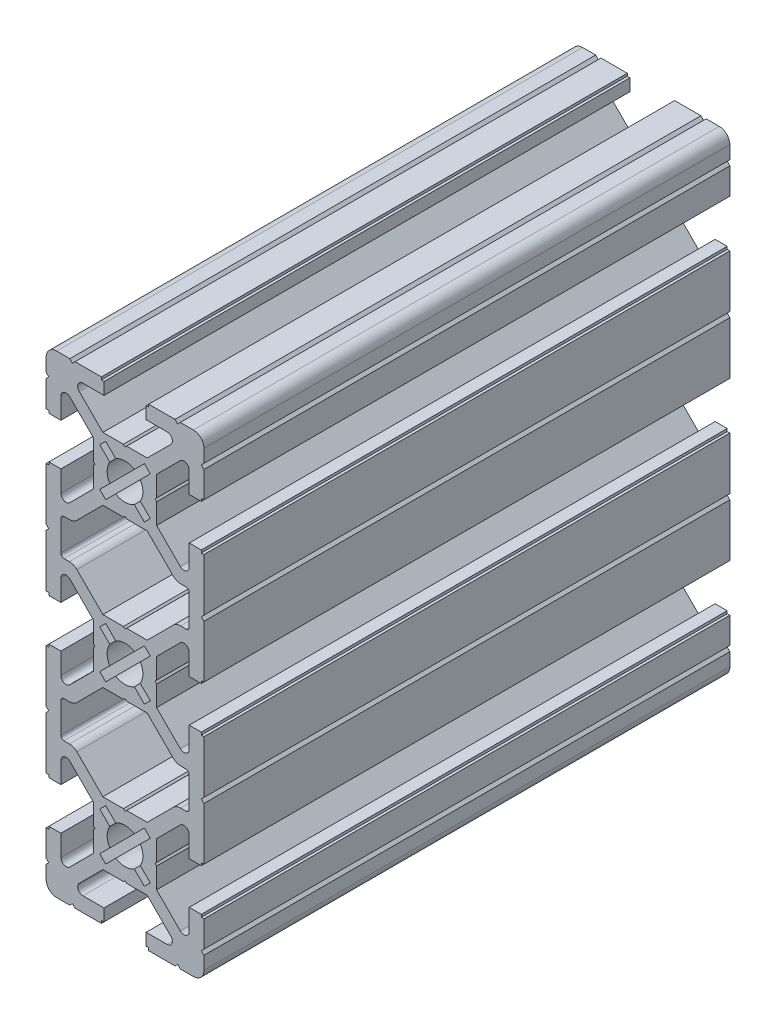
SolidWorks part; units mm, degrees
ref_plane "Ön Düzlem" through (0, 0, 0) normal (0, 0, 1) x (1, 0, 0)
ref_plane "Üst Düzlem" through (0, 0, 0) normal (0, 1, 0) x (1, 0, 0)
ref_plane "Sağ Düzlem" through (0, 0, 0) normal (1, 0, 0) x (0, 0, -1)
ref_plane "Düzlem1" through (0, 0, 100) normal (0, 0, 1) x (1, 0, 0)
sketch "Çizim1" plane through (0, 0, 100) normal (0, 0, 1) x (1, 0, 0)
  line L0 (-2.9023, 31.771) -> (-4.8083, 33.677)
  line L1 (-4.8083, 33.677) -> (-3.677, 34.8083)
  line L2 (-3.677, 34.8083) -> (-1.771, 32.9023)
  line L3 (1.771, 32.9023) -> (3.677, 34.8083)
  line L4 (3.677, 34.8083) -> (4.8083, 33.677)
  line L5 (4.8083, 33.677) -> (2.9023, 31.771)
  line L6 (2.9023, 28.229) -> (4.8083, 26.323)
  line L7 (4.8083, 26.323) -> (3.677, 25.1917)
  line L8 (3.677, 25.1917) -> (1.771, 27.0977)
  line L9 (-1.771, 27.0977) -> (-3.677, 25.1917)
  line L10 (-3.677, 25.1917) -> (-4.8083, 26.323)
  line L11 (-4.8083, 26.323) -> (-2.9023, 28.229)
  line L12 (-2.9023, 1.771) -> (-4.8083, 3.677)
  line L13 (-4.8083, 3.677) -> (-3.677, 4.8083)
  line L14 (-3.677, 4.8083) -> (-1.771, 2.9023)
  line L15 (1.771, 2.9023) -> (3.677, 4.8083)
  line L16 (3.677, 4.8083) -> (4.8083, 3.677)
  line L17 (4.8083, 3.677) -> (2.9023, 1.771)
  line L18 (2.9023, -1.771) -> (4.8083, -3.677)
  line L19 (4.8083, -3.677) -> (3.677, -4.8083)
  line L20 (3.677, -4.8083) -> (1.771, -2.9023)
  line L21 (-1.771, -2.9023) -> (-3.677, -4.8083)
  line L22 (-3.677, -4.8083) -> (-4.8083, -3.677)
  line L23 (-4.8083, -3.677) -> (-2.9023, -1.771)
  line L24 (-2.9023, -28.229) -> (-4.8083, -26.323)
  line L25 (-4.8083, -26.323) -> (-3.677, -25.1917)
  line L26 (-3.677, -25.1917) -> (-1.771, -27.0977)
  line L27 (1.771, -27.0977) -> (3.677, -25.1917)
  line L28 (3.677, -25.1917) -> (4.8083, -26.323)
  line L29 (4.8083, -26.323) -> (2.9023, -28.229)
  line L30 (2.9023, -31.771) -> (4.8083, -33.677)
  line L31 (4.8083, -33.677) -> (3.677, -34.8083)
  line L32 (3.677, -34.8083) -> (1.771, -32.9023)
  line L33 (-1.771, -32.9023) -> (-3.677, -34.8083)
  line L34 (-3.677, -34.8083) -> (-4.8083, -33.677)
  line L35 (-4.8083, -33.677) -> (-2.9023, -31.771)
  line L36 (-9.1584, 19.0558) -> (-4.2142, 24)
  line L37 (-4.2142, 24) -> (-0.3125, 24)
  line L38 (-0.3125, 24) -> (0, 24.3)
  line L39 (0, 24.3) -> (0.3125, 24)
  line L40 (0.3125, 24) -> (4.2142, 24)
  line L41 (4.2142, 24) -> (9.1584, 19.0558)
  line L42 (10.5726, 18.47) -> (11.6, 18.47)
  line L43 (12.2, 17.87) -> (12.2, 12.13)
  line L44 (11.6, 11.53) -> (10.5726, 11.53)
  line L45 (9.1584, 10.9442) -> (4.2142, 6)
  line L46 (4.2142, 6) -> (0.3125, 6)
  line L47 (0.3125, 6) -> (0, 5.7)
  line L48 (0, 5.7) -> (-0.3125, 6)
  line L49 (-0.3125, 6) -> (-4.2142, 6)
  line L50 (-4.2142, 6) -> (-9.1584, 10.9442)
  line L51 (-10.5726, 11.53) -> (-11.6, 11.53)
  line L52 (-12.2, 12.13) -> (-12.2, 17.87)
  line L53 (-11.6, 18.47) -> (-10.5726, 18.47)
  line L54 (-9.1584, -10.9442) -> (-4.2142, -6)
  line L55 (-4.2142, -6) -> (-0.3125, -6)
  line L56 (-0.3125, -6) -> (0, -5.7)
  line L57 (0, -5.7) -> (0.3125, -6)
  line L58 (0.3125, -6) -> (4.2142, -6)
  line L59 (4.2142, -6) -> (9.1584, -10.9442)
  line L60 (10.5726, -11.53) -> (11.6, -11.53)
  line L61 (12.2, -12.13) -> (12.2, -17.87)
  line L62 (11.6, -18.47) -> (10.5726, -18.47)
  line L63 (9.1584, -19.0558) -> (4.2142, -24)
  line L64 (4.2142, -24) -> (0.3125, -24)
  line L65 (0.3125, -24) -> (0, -24.3)
  line L66 (0, -24.3) -> (-0.3125, -24)
  line L67 (-0.3125, -24) -> (-4.2142, -24)
  line L68 (-4.2142, -24) -> (-9.1584, -19.0558)
  line L69 (-10.5726, -18.47) -> (-11.6, -18.47)
  line L70 (-12.2, -17.87) -> (-12.2, -12.13)
  line L71 (-11.6, -11.53) -> (-10.5726, -11.53)
  line L72 (-4.2142, 36) -> (-8.7071, 40.4929)
  line L73 (-8, 42.2) -> (-4, 42.2)
  line L74 (-4, 42.2) -> (-4, 44.5)
  line L75 (-4, 44.5) -> (-4.5, 44.5)
  line L76 (-4.5, 44.5) -> (-4.5, 45)
  line L77 (-4.5, 45) -> (-9.5, 45)
  line L78 (-9.5, 45) -> (-10, 44.5)
  line L79 (-10, 44.5) -> (-10.5, 45)
  line L80 (-10.5, 45) -> (-13, 45)
  line L81 (-15, 43) -> (-15, 40.5)
  line L82 (-15, 40.5) -> (-14.5, 40)
  line L83 (-14.5, 40) -> (-15, 39.5)
  line L84 (-15, 39.5) -> (-15, 34.5)
  line L85 (-15, 34.5) -> (-14.5, 34.5)
  line L86 (-14.5, 34.5) -> (-14.5, 34)
  line L87 (-14.5, 34) -> (-12.2, 34)
  line L88 (-12.2, 34) -> (-12.2, 38)
  line L89 (-10.4929, 38.7071) -> (-6, 34.2142)
  line L90 (-6, 34.2142) -> (-6, 30.3125)
  line L91 (-6, 30.3125) -> (-5.7, 30)
  line L92 (-5.7, 30) -> (-6, 29.6875)
  line L93 (-6, 29.6875) -> (-6, 25.7858)
  line L94 (-6, 25.7858) -> (-10.4929, 21.2929)
  line L95 (-12.2, 22) -> (-12.2, 26)
  line L96 (-12.2, 26) -> (-14.5, 26)
  line L97 (-14.5, 26) -> (-14.5, 25.5)
  line L98 (-14.5, 25.5) -> (-15, 25.5)
  line L99 (-15, 25.5) -> (-15, 15.5)
  line L100 (-15, 15.5) -> (-14.5, 15)
  line L101 (-14.5, 15) -> (-15, 14.5)
  line L102 (-15, 14.5) -> (-15, 4.5)
  line L103 (-15, 4.5) -> (-14.5, 4.5)
  line L104 (-14.5, 4.5) -> (-14.5, 4)
  line L105 (-14.5, 4) -> (-12.2, 4)
  line L106 (-12.2, 4) -> (-12.2, 8)
  line L107 (-10.4929, 8.7071) -> (-6, 4.2142)
  line L108 (-6, 4.2142) -> (-6, 0.3125)
  line L109 (-6, 0.3125) -> (-5.7, 0)
  line L110 (-5.7, 0) -> (-6, -0.3125)
  line L111 (-6, -0.3125) -> (-6, -4.2142)
  line L112 (-6, -4.2142) -> (-10.4929, -8.7071)
  line L113 (-12.2, -8) -> (-12.2, -4)
  line L114 (-12.2, -4) -> (-14.5, -4)
  line L115 (-14.5, -4) -> (-14.5, -4.5)
  line L116 (-14.5, -4.5) -> (-15, -4.5)
  line L117 (-15, -4.5) -> (-15, -14.5)
  line L118 (-15, -14.5) -> (-14.5, -15)
  line L119 (-14.5, -15) -> (-15, -15.5)
  line L120 (-15, -15.5) -> (-15, -25.5)
  line L121 (-15, -25.5) -> (-14.5, -25.5)
  line L122 (-14.5, -25.5) -> (-14.5, -26)
  line L123 (-14.5, -26) -> (-12.2, -26)
  line L124 (-12.2, -26) -> (-12.2, -22)
  line L125 (-10.4929, -21.2929) -> (-6, -25.7858)
  line L126 (-6, -25.7858) -> (-6, -29.6875)
  line L127 (-6, -29.6875) -> (-5.7, -30)
  line L128 (-5.7, -30) -> (-6, -30.3125)
  line L129 (-6, -30.3125) -> (-6, -34.2142)
  line L130 (-6, -34.2142) -> (-10.4929, -38.7071)
  line L131 (-12.2, -38) -> (-12.2, -34)
  line L132 (-12.2, -34) -> (-14.5, -34)
  line L133 (-14.5, -34) -> (-14.5, -34.5)
  line L134 (-14.5, -34.5) -> (-15, -34.5)
  line L135 (-15, -34.5) -> (-15, -39.5)
  line L136 (-15, -39.5) -> (-14.5, -40)
  line L137 (-14.5, -40) -> (-15, -40.5)
  line L138 (-15, -40.5) -> (-15, -43)
  line L139 (-13, -45) -> (-10.5, -45)
  line L140 (-10.5, -45) -> (-10, -44.5)
  line L141 (-10, -44.5) -> (-9.5, -45)
  line L142 (-9.5, -45) -> (-4.5, -45)
  line L143 (-4.5, -45) -> (-4.5, -44.5)
  line L144 (-4.5, -44.5) -> (-4, -44.5)
  line L145 (-4, -44.5) -> (-4, -42.2)
  line L146 (-4, -42.2) -> (-8, -42.2)
  line L147 (-8.7071, -40.4929) -> (-4.2142, -36)
  line L148 (-4.2142, -36) -> (-0.3125, -36)
  line L149 (-0.3125, -36) -> (0, -35.7)
  line L150 (0, -35.7) -> (0.3125, -36)
  line L151 (0.3125, -36) -> (4.2142, -36)
  line L152 (4.2142, -36) -> (8.7071, -40.4929)
  line L153 (8, -42.2) -> (4, -42.2)
  line L154 (4, -42.2) -> (4, -44.5)
  line L155 (4, -44.5) -> (4.5, -44.5)
  line L156 (4.5, -44.5) -> (4.5, -45)
  line L157 (4.5, -45) -> (9.5, -45)
  line L158 (9.5, -45) -> (10, -44.5)
  line L159 (10, -44.5) -> (10.5, -45)
  line L160 (10.5, -45) -> (13, -45)
  line L161 (15, -43) -> (15, -40.5)
  line L162 (15, -40.5) -> (14.5, -40)
  line L163 (14.5, -40) -> (15, -39.5)
  line L164 (15, -39.5) -> (15, -34.5)
  line L165 (15, -34.5) -> (14.5, -34.5)
  line L166 (14.5, -34.5) -> (14.5, -34)
  line L167 (14.5, -34) -> (12.2, -34)
  line L168 (12.2, -34) -> (12.2, -38)
  line L169 (10.4929, -38.7071) -> (6, -34.2142)
  line L170 (6, -34.2142) -> (6, -30.3125)
  line L171 (6, -30.3125) -> (5.7, -30)
  line L172 (5.7, -30) -> (6, -29.6875)
  line L173 (6, -29.6875) -> (6, -25.7858)
  line L174 (6, -25.7858) -> (10.4929, -21.2929)
  line L175 (12.2, -22) -> (12.2, -26)
  line L176 (12.2, -26) -> (14.5, -26)
  line L177 (14.5, -26) -> (14.5, -25.5)
  line L178 (14.5, -25.5) -> (15, -25.5)
  line L179 (15, -25.5) -> (15, -15.5)
  line L180 (15, -15.5) -> (14.5, -15)
  line L181 (14.5, -15) -> (15, -14.5)
  line L182 (15, -14.5) -> (15, -4.5)
  line L183 (15, -4.5) -> (14.5, -4.5)
  line L184 (14.5, -4.5) -> (14.5, -4)
  line L185 (14.5, -4) -> (12.2, -4)
  line L186 (12.2, -4) -> (12.2, -8)
  line L187 (10.4929, -8.7071) -> (6, -4.2142)
  line L188 (6, -4.2142) -> (6, -0.3125)
  line L189 (6, -0.3125) -> (5.7, 0)
  line L190 (5.7, 0) -> (6, 0.3125)
  line L191 (6, 0.3125) -> (6, 4.2142)
  line L192 (6, 4.2142) -> (10.4929, 8.7071)
  line L193 (12.2, 8) -> (12.2, 4)
  line L194 (12.2, 4) -> (14.5, 4)
  line L195 (14.5, 4) -> (14.5, 4.5)
  line L196 (14.5, 4.5) -> (15, 4.5)
  line L197 (15, 4.5) -> (15, 14.5)
  line L198 (15, 14.5) -> (14.5, 15)
  line L199 (14.5, 15) -> (15, 15.5)
  line L200 (15, 15.5) -> (15, 25.5)
  line L201 (15, 25.5) -> (14.5, 25.5)
  line L202 (14.5, 25.5) -> (14.5, 26)
  line L203 (14.5, 26) -> (12.2, 26)
  line L204 (12.2, 26) -> (12.2, 22)
  line L205 (10.4929, 21.2929) -> (6, 25.7858)
  line L206 (6, 25.7858) -> (6, 29.6875)
  line L207 (6, 29.6875) -> (5.7, 30)
  line L208 (5.7, 30) -> (6, 30.3125)
  line L209 (6, 30.3125) -> (6, 34.2142)
  line L210 (6, 34.2142) -> (10.4929, 38.7071)
  line L211 (12.2, 38) -> (12.2, 34)
  line L212 (12.2, 34) -> (14.5, 34)
  line L213 (14.5, 34) -> (14.5, 34.5)
  line L214 (14.5, 34.5) -> (15, 34.5)
  line L215 (15, 34.5) -> (15, 39.5)
  line L216 (15, 39.5) -> (14.5, 40)
  line L217 (14.5, 40) -> (15, 40.5)
  line L218 (15, 40.5) -> (15, 43)
  line L219 (13, 45) -> (10.5, 45)
  line L220 (10.5, 45) -> (10, 44.5)
  line L221 (10, 44.5) -> (9.5, 45)
  line L222 (9.5, 45) -> (4.5, 45)
  line L223 (4.5, 45) -> (4.5, 44.5)
  line L224 (4.5, 44.5) -> (4, 44.5)
  line L225 (4, 44.5) -> (4, 42.2)
  line L226 (4, 42.2) -> (8, 42.2)
  line L227 (8.7071, 40.4929) -> (4.2142, 36)
  line L228 (4.2142, 36) -> (0.3125, 36)
  line L229 (0.3125, 36) -> (0, 35.7)
  line L230 (0, 35.7) -> (-0.3125, 36)
  line L231 (-0.3125, 36) -> (-4.2142, 36)
  arc A0 (-1.771, 32.9023) -> (1.771, 32.9023) centre (0, 30) cw
  arc A1 (2.9023, 31.771) -> (2.9023, 28.229) centre (0, 30) cw
  arc A2 (1.771, 27.0977) -> (-1.771, 27.0977) centre (0, 30) cw
  arc A3 (-2.9023, 28.229) -> (-2.9023, 31.771) centre (0, 30) cw
  arc A4 (-1.771, 2.9023) -> (1.771, 2.9023) centre (0, 0) cw
  arc A5 (2.9023, 1.771) -> (2.9023, -1.771) centre (0, 0) cw
  arc A6 (1.771, -2.9023) -> (-1.771, -2.9023) centre (0, 0) cw
  arc A7 (-2.9023, -1.771) -> (-2.9023, 1.771) centre (0, 0) cw
  arc A8 (-1.771, -27.0977) -> (1.771, -27.0977) centre (0, -30) cw
  arc A9 (2.9023, -28.229) -> (2.9023, -31.771) centre (0, -30) cw
  arc A10 (1.771, -32.9023) -> (-1.771, -32.9023) centre (0, -30) cw
  arc A11 (-2.9023, -31.771) -> (-2.9023, -28.229) centre (0, -30) cw
  arc A12 (9.1584, 19.0558) -> (10.5726, 18.47) centre (10.5726, 20.47) ccw
  arc A13 (11.6, 18.47) -> (12.2, 17.87) centre (11.6, 17.87) cw
  arc A14 (12.2, 12.13) -> (11.6, 11.53) centre (11.6, 12.13) cw
  arc A15 (10.5726, 11.53) -> (9.1584, 10.9442) centre (10.5726, 9.53) ccw
  arc A16 (-9.1584, 10.9442) -> (-10.5726, 11.53) centre (-10.5726, 9.53) ccw
  arc A17 (-11.6, 11.53) -> (-12.2, 12.13) centre (-11.6, 12.13) cw
  arc A18 (-12.2, 17.87) -> (-11.6, 18.47) centre (-11.6, 17.87) cw
  arc A19 (-10.5726, 18.47) -> (-9.1584, 19.0558) centre (-10.5726, 20.47) ccw
  arc A20 (9.1584, -10.9442) -> (10.5726, -11.53) centre (10.5726, -9.53) ccw
  arc A21 (11.6, -11.53) -> (12.2, -12.13) centre (11.6, -12.13) cw
  arc A22 (12.2, -17.87) -> (11.6, -18.47) centre (11.6, -17.87) cw
  arc A23 (10.5726, -18.47) -> (9.1584, -19.0558) centre (10.5726, -20.47) ccw
  arc A24 (-9.1584, -19.0558) -> (-10.5726, -18.47) centre (-10.5726, -20.47) ccw
  arc A25 (-11.6, -18.47) -> (-12.2, -17.87) centre (-11.6, -17.87) cw
  arc A26 (-12.2, -12.13) -> (-11.6, -11.53) centre (-11.6, -12.13) cw
  arc A27 (-10.5726, -11.53) -> (-9.1584, -10.9442) centre (-10.5726, -9.53) ccw
  arc A28 (-8.7071, 40.4929) -> (-8, 42.2) centre (-8, 41.2) cw
  arc A29 (-13, 45) -> (-15, 43) centre (-13, 43) ccw
  arc A30 (-12.2, 38) -> (-10.4929, 38.7071) centre (-11.2, 38) cw
  arc A31 (-10.4929, 21.2929) -> (-12.2, 22) centre (-11.2, 22) cw
  arc A32 (-12.2, 8) -> (-10.4929, 8.7071) centre (-11.2, 8) cw
  arc A33 (-10.4929, -8.7071) -> (-12.2, -8) centre (-11.2, -8) cw
  arc A34 (-12.2, -22) -> (-10.4929, -21.2929) centre (-11.2, -22) cw
  arc A35 (-10.4929, -38.7071) -> (-12.2, -38) centre (-11.2, -38) cw
  arc A36 (-15, -43) -> (-13, -45) centre (-13, -43) ccw
  arc A37 (-8, -42.2) -> (-8.7071, -40.4929) centre (-8, -41.2) cw
  arc A38 (8.7071, -40.4929) -> (8, -42.2) centre (8, -41.2) cw
  arc A39 (13, -45) -> (15, -43) centre (13, -43) ccw
  arc A40 (12.2, -38) -> (10.4929, -38.7071) centre (11.2, -38) cw
  arc A41 (10.4929, -21.2929) -> (12.2, -22) centre (11.2, -22) cw
  arc A42 (12.2, -8) -> (10.4929, -8.7071) centre (11.2, -8) cw
  arc A43 (10.4929, 8.7071) -> (12.2, 8) centre (11.2, 8) cw
  arc A44 (12.2, 22) -> (10.4929, 21.2929) centre (11.2, 22) cw
  arc A45 (10.4929, 38.7071) -> (12.2, 38) centre (11.2, 38) cw
  arc A46 (15, 43) -> (13, 45) centre (13, 43) ccw
  arc A47 (8, 42.2) -> (8.7071, 40.4929) centre (8, 41.2) cw
extrude "Yükseklik-Ekstrüzyon1" add sketch "Çizim1" against normal blind 100
